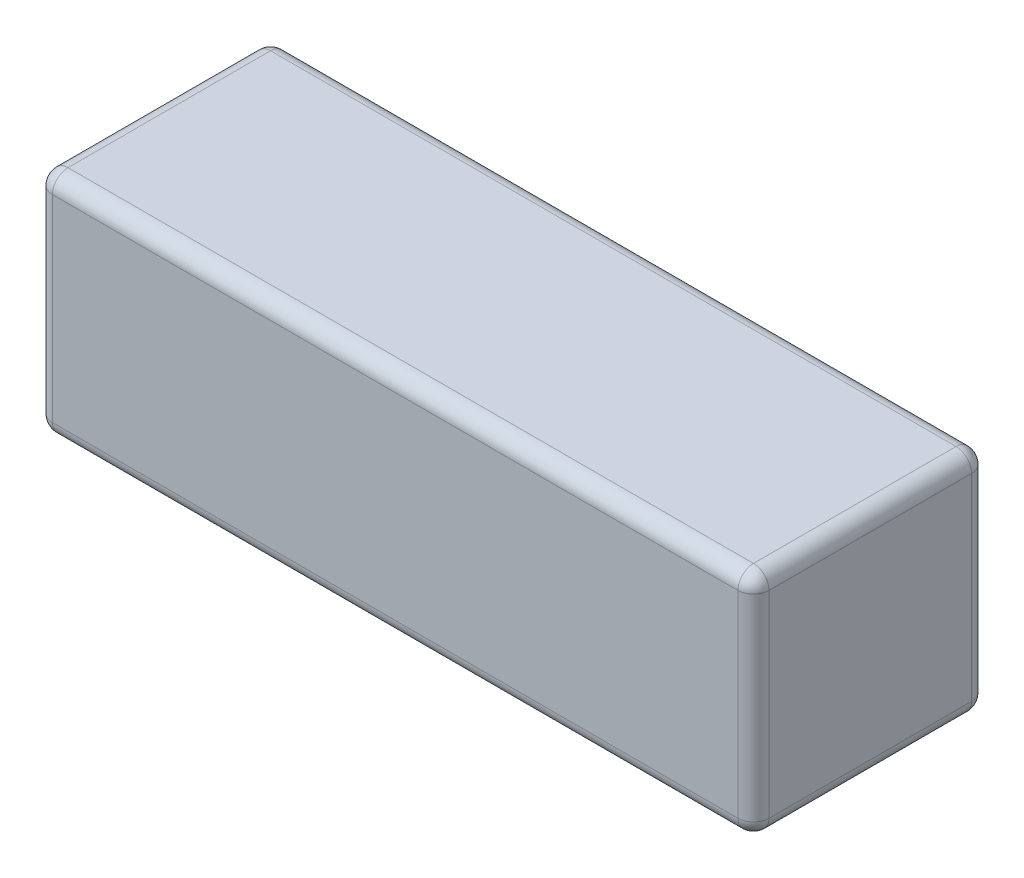
SolidWorks part; units mm, degrees
ref_plane "前视基准面" through (0, 0, 0) normal (0, 0, 1) x (1, 0, 0)
ref_plane "上视基准面" through (0, 0, 0) normal (0, 1, 0) x (1, 0, 0)
ref_plane "右视基准面" through (0, 0, 0) normal (1, 0, 0) x (0, 0, -1)
sketch "草图1" plane through (0, 0, 0) normal (0, 0, 1) x (1, 0, 0)
  line L1 (69, -22) -> (-69, -22)
  line L2 (69, -22) -> (69, 22)
  line L3 (69, 22) -> (-69, 22)
  line L4 (-69, -22) -> (-69, 22)
  line L5 (69, -22) -> (-69, 22) construction
  line L6 (69, 22) -> (-69, -22) construction
  point P0 (0, 0)
  dimension "D1" = 44
  dimension "D2" = 138
extrude "凸台-拉伸1" add sketch "草图1" along normal blind 45
fillet "圆角1" radius 3 12 edges at (-69, 22, 22.5) (0, 22, 0) (-69, 0, 0) (-69, -22, 22.5) (0, -22, 0) (69, -22, 22.5) (69, 22, 22.5) (69, 0, 0) (0, 22, 45) (69, 0, 45) (0, -22, 45) (-69, 0, 45)
